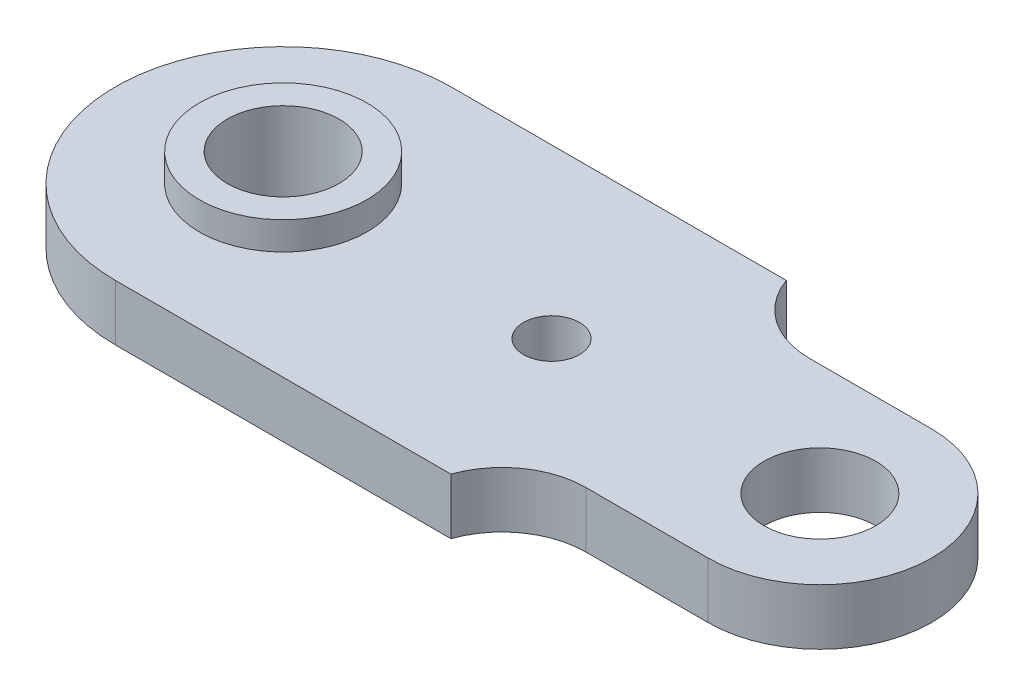
SolidWorks part; units mm, degrees
ref_plane "Front Plane" through (0, 0, 0) normal (0, 0, 1) x (1, 0, 0)
ref_plane "Top Plane" through (0, 0, 0) normal (0, 1, 0) x (1, 0, 0)
ref_plane "Right Plane" through (0, 0, 0) normal (1, 0, 0) x (0, 0, -1)
sketch "Sketch1" plane through (0, 0, 0) normal (0, 1, 0) x (1, 0, 0)
  line L0 (-48, 30) -> (12, 30)
  line L1 (-48, -30) -> (12, -30)
  line L2 (48, 20) -> (26.1421, 20)
  line L3 (48, 0) -> (-48, 0) construction
  line L4 (48, -20) -> (26.1421, -20)
  circle A0 centre (0, 0) radius 5
  circle A1 centre (48, 0) radius 10
  circle A2 centre (-48, 0) radius 10
  circle A3 centre (-48, 0) radius 30
  circle A4 centre (48, 0) radius 20
  circle A5 centre (26.1421, 35) radius 15
  circle A6 centre (26.1421, -35) radius 15
  point P13 (47.858, 5.2192)
  point P14 (48, 0)
  point P23 (0, 0)
  point P24 (48, 0)
  dimension "D1" = 10
  dimension "D2" = 20
  dimension "D3" = 40
  dimension "D4" = 60
  dimension "D5" = 20
  dimension "D10" = 30
  dimension "D6" = 48
  dimension "D7" = 96
  dimension "D8" = 60
  dimension "D9" = 60
  dimension "D12" = 30
extrude "Boss-Extrude1" add sketch "Sketch1" along normal blind 10
sketch "Sketch2" plane through (0, 10, 0) normal (0, 1, 0) x (1, 0, 0)
  circle A0 centre (-48, 0) radius 15
  circle A1 centre (-48, 0) radius 10
  dimension "D1" = 30
extrude "Boss-Extrude2" add sketch "Sketch2" along normal blind 5
